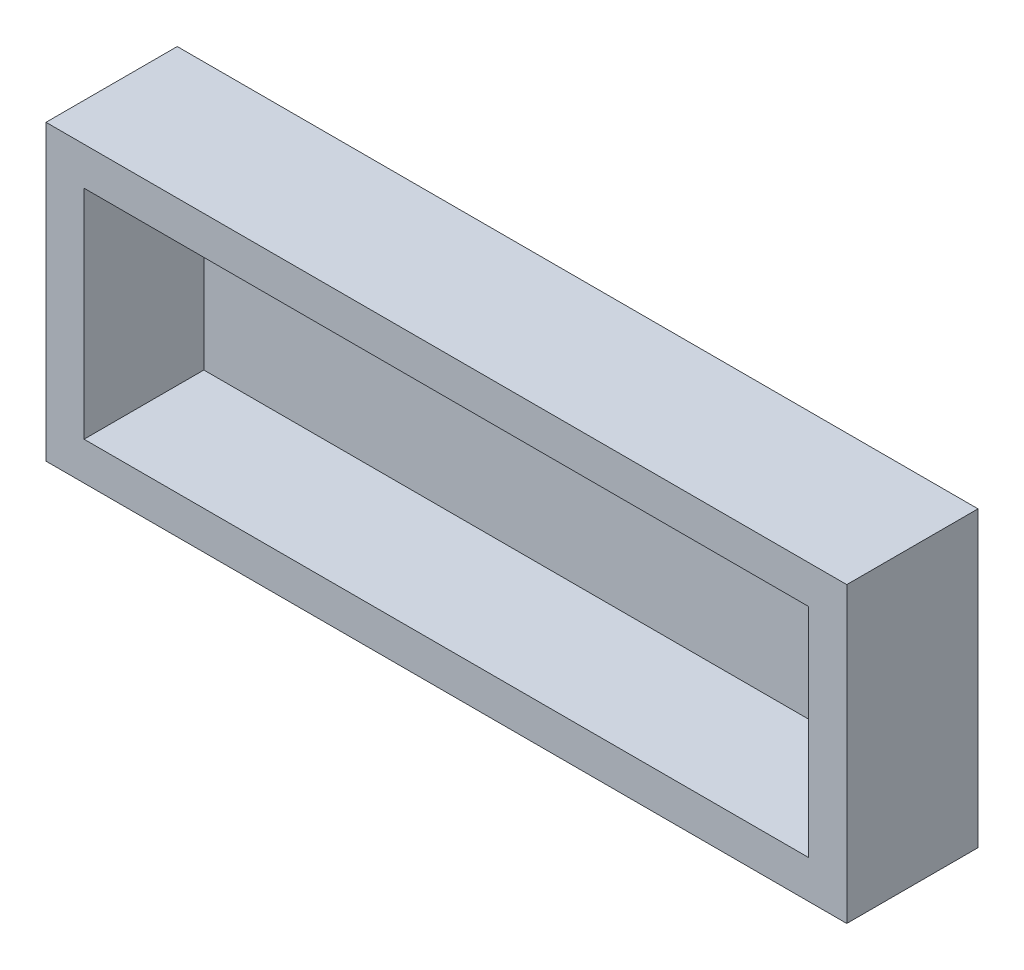
SolidWorks part; units mm, degrees
ref_plane "Front Plane" through (0, 0, 0) normal (0, 0, 1) x (1, 0, 0)
ref_plane "Top Plane" through (0, 0, 0) normal (0, 1, 0) x (1, 0, 0)
ref_plane "Right Plane" through (0, 0, 0) normal (1, 0, 0) x (0, 0, -1)
sketch "Model" plane through (0, 0, 0) normal (0, 0, 1) x (1, 0, 0)
  line L0 (188.597, 57.4075) -> (188.753, 57.4008)
  line L1 (188.753, 57.4008) -> (188.908, 57.3828)
  line L2 (188.908, 57.3828) -> (189.063, 57.3525)
  line L3 (189.063, 57.3525) -> (189.214, 57.3098)
  line L4 (189.214, 57.3098) -> (189.362, 57.2548)
  line L5 (189.362, 57.2548) -> (189.504, 57.1899)
  line L6 (189.504, 57.1899) -> (189.64, 57.113)
  line L7 (189.64, 57.113) -> (189.771, 57.0258)
  line L8 (189.771, 57.0258) -> (189.895, 56.9281)
  line L9 (189.895, 56.9281) -> (190.011, 56.8219)
  line L10 (190.011, 56.8219) -> (190.117, 56.7062)
  line L11 (190.117, 56.7062) -> (190.215, 56.5838)
  line L12 (190.215, 56.5838) -> (190.302, 56.4526)
  line L13 (190.302, 56.4526) -> (190.379, 56.315)
  line L14 (190.379, 56.315) -> (190.444, 56.1728)
  line L15 (190.444, 56.1728) -> (190.499, 56.0268)
  line L16 (190.499, 56.0268) -> (190.54, 55.874)
  line L17 (190.54, 55.874) -> (190.572, 55.7209)
  line L18 (190.572, 55.7209) -> (190.59, 55.5639)
  line L19 (190.59, 55.5639) -> (190.596, 55.4069)
  line L20 (190.596, 55.4069) -> (190.596, 2.2572)
  line L21 (190.596, 2.2572) -> (190.59, 2.1001)
  line L22 (190.59, 2.1001) -> (190.572, 1.9444)
  line L23 (190.572, 1.9444) -> (190.54, 1.7901)
  line L24 (190.54, 1.7901) -> (190.499, 1.6385)
  line L25 (190.499, 1.6385) -> (190.444, 1.491)
  line L26 (190.444, 1.491) -> (190.379, 1.3491)
  line L27 (190.379, 1.3491) -> (190.302, 1.2127)
  line L28 (190.302, 1.2127) -> (190.215, 1.0818)
  line L29 (190.215, 1.0818) -> (190.117, 0.9577)
  line L30 (190.117, 0.9577) -> (190.011, 0.842)
  line L31 (190.011, 0.842) -> (189.895, 0.7359)
  line L32 (189.895, 0.7359) -> (189.771, 0.638)
  line L33 (189.771, 0.638) -> (189.64, 0.5512)
  line L34 (189.64, 0.5512) -> (189.504, 0.474)
  line L35 (189.504, 0.474) -> (189.362, 0.4093)
  line L36 (189.362, 0.4093) -> (189.214, 0.3542)
  line L37 (189.214, 0.3542) -> (189.063, 0.3128)
  line L38 (189.063, 0.3128) -> (188.908, 0.2811)
  line L39 (188.908, 0.2811) -> (188.753, 0.2632)
  line L40 (188.753, 0.2632) -> (188.597, 0.2563)
  line L41 (188.597, 0.2563) -> (2.096, 0.2577)
  line L42 (2.096, 0.2577) -> (1.9389, 0.2632)
  line L43 (1.9389, 0.2632) -> (1.7818, 0.2811)
  line L44 (1.7818, 0.2811) -> (1.6288, 0.3128)
  line L45 (1.6288, 0.3128) -> (1.4759, 0.3542)
  line L46 (1.4759, 0.3542) -> (1.3298, 0.4093)
  line L47 (1.3298, 0.4093) -> (1.1879, 0.474)
  line L48 (1.1879, 0.474) -> (1.0501, 0.5512)
  line L49 (1.0501, 0.5512) -> (0.9192, 0.638)
  line L50 (0.9192, 0.638) -> (0.7965, 0.7359)
  line L51 (0.7965, 0.7359) -> (0.6808, 0.842)
  line L52 (0.6808, 0.842) -> (0.5746, 0.9577)
  line L53 (0.5746, 0.9577) -> (0.4768, 1.0818)
  line L54 (0.4768, 1.0818) -> (0.39, 1.2127)
  line L55 (0.39, 1.2127) -> (0.3128, 1.3491)
  line L56 (0.3128, 1.3491) -> (0.248, 1.491)
  line L57 (0.248, 1.491) -> (0.1929, 1.6385)
  line L58 (0.1929, 1.6385) -> (0.1502, 1.7901)
  line L59 (0.1502, 1.7901) -> (0.1199, 1.9444)
  line L60 (0.1199, 1.9444) -> (0.102, 2.1001)
  line L61 (0.102, 2.1001) -> (0.0951, 2.2572)
  line L62 (0.0951, 2.2572) -> (0.0951, 55.4069)
  line L63 (0.0951, 55.4069) -> (0.102, 55.5639)
  line L64 (0.102, 55.5639) -> (0.1199, 55.7209)
  line L65 (0.1199, 55.7209) -> (0.1502, 55.874)
  line L66 (0.1502, 55.874) -> (0.1929, 56.0268)
  line L67 (0.1929, 56.0268) -> (0.248, 56.1728)
  line L68 (0.248, 56.1728) -> (0.3128, 56.315)
  line L69 (0.3128, 56.315) -> (0.39, 56.4526)
  line L70 (0.39, 56.4526) -> (0.4768, 56.5838)
  line L71 (0.4768, 56.5838) -> (0.5746, 56.7062)
  line L72 (0.5746, 56.7062) -> (0.6808, 56.8219)
  line L73 (0.6808, 56.8219) -> (0.7965, 56.9281)
  line L74 (0.7965, 56.9281) -> (0.9192, 57.0258)
  line L75 (0.9192, 57.0258) -> (1.0501, 57.113)
  line L76 (1.0501, 57.113) -> (1.1879, 57.1899)
  line L77 (1.1879, 57.1899) -> (1.3298, 57.2548)
  line L78 (1.3298, 57.2548) -> (1.4759, 57.3098)
  line L79 (1.4759, 57.3098) -> (1.6288, 57.3525)
  line L80 (1.6288, 57.3525) -> (1.7818, 57.3828)
  line L81 (1.7818, 57.3828) -> (1.9389, 57.4008)
  line L82 (1.9389, 57.4008) -> (2.096, 57.4075)
  line L83 (2.096, 57.4075) -> (188.597, 57.4075)
  line L84 (174.071, 16.7817) -> (188.07, 16.7817)
  line L85 (188.07, 16.7817) -> (188.07, 2.7823)
  line L86 (188.07, 2.7823) -> (174.071, 2.7823)
  line L87 (174.071, 2.7823) -> (174.071, 16.7817)
  line L88 (155.021, 16.7817) -> (169.02, 16.7817)
  line L89 (169.02, 16.7817) -> (169.02, 2.7823)
  line L90 (169.02, 2.7823) -> (155.021, 2.7823)
  line L91 (155.021, 2.7823) -> (155.021, 16.7817)
  line L92 (135.971, 16.7817) -> (149.97, 16.7817)
  line L93 (149.97, 16.7817) -> (149.97, 2.7823)
  line L94 (149.97, 2.7823) -> (135.971, 2.7823)
  line L95 (135.971, 2.7823) -> (135.971, 16.7817)
  line L96 (116.92, 16.7817) -> (130.92, 16.7817)
  line L97 (130.92, 16.7817) -> (130.92, 2.7823)
  line L98 (130.92, 2.7823) -> (116.92, 2.7823)
  line L99 (116.92, 2.7823) -> (116.92, 16.7817)
  line L100 (97.8697, 16.7817) -> (111.869, 16.7817)
  line L101 (111.869, 16.7817) -> (111.869, 2.7823)
  line L102 (111.869, 2.7823) -> (97.8697, 2.7823)
  line L103 (97.8697, 2.7823) -> (97.8697, 16.7817)
  line L104 (78.8211, 16.7817) -> (92.8204, 16.7817)
  line L105 (92.8204, 16.7817) -> (92.8204, 2.7823)
  line L106 (92.8204, 2.7823) -> (78.8211, 2.7823)
  line L107 (78.8211, 2.7823) -> (78.8211, 16.7817)
  line L108 (59.7711, 16.7817) -> (73.7704, 16.7817)
  line L109 (73.7704, 16.7817) -> (73.7704, 2.7823)
  line L110 (73.7704, 2.7823) -> (59.7711, 2.7823)
  line L111 (59.7711, 2.7823) -> (59.7711, 16.7817)
  line L112 (40.7211, 16.7817) -> (54.7204, 16.7817)
  line L113 (54.7204, 16.7817) -> (54.7204, 2.7823)
  line L114 (54.7204, 2.7823) -> (40.7211, 2.7823)
  line L115 (40.7211, 2.7823) -> (40.7211, 16.7817)
  line L116 (21.671, 16.7817) -> (35.6704, 16.7817)
  line L117 (35.6704, 16.7817) -> (35.6704, 2.7823)
  line L118 (35.6704, 2.7823) -> (21.671, 2.7823)
  line L119 (21.671, 2.7823) -> (21.671, 16.7817)
  line L120 (2.621, 16.7817) -> (16.6205, 16.7817)
  line L121 (16.6205, 16.7817) -> (16.6205, 2.7823)
  line L122 (16.6205, 2.7823) -> (2.621, 2.7823)
  line L123 (2.621, 2.7823) -> (2.621, 16.7817)
  line L124 (174.071, 35.8316) -> (188.07, 35.8316)
  line L125 (188.07, 35.8316) -> (188.07, 21.8323)
  line L126 (188.07, 21.8323) -> (174.071, 21.8323)
  line L127 (174.071, 21.8323) -> (174.071, 35.8316)
  line L128 (155.021, 35.8316) -> (169.02, 35.8316)
  line L129 (169.02, 35.8316) -> (169.02, 21.8323)
  line L130 (169.02, 21.8323) -> (155.021, 21.8323)
  line L131 (155.021, 21.8323) -> (155.021, 35.8316)
  line L132 (135.971, 35.8316) -> (149.97, 35.8316)
  line L133 (149.97, 35.8316) -> (149.97, 21.8323)
  line L134 (149.97, 21.8323) -> (135.971, 21.8323)
  line L135 (135.971, 21.8323) -> (135.971, 35.8316)
  line L136 (116.92, 35.8316) -> (130.92, 35.8316)
  line L137 (130.92, 35.8316) -> (130.92, 21.8323)
  line L138 (130.92, 21.8323) -> (116.92, 21.8323)
  line L139 (116.92, 21.8323) -> (116.92, 35.8316)
  line L140 (97.8697, 35.8316) -> (111.869, 35.8316)
  line L141 (111.869, 35.8316) -> (111.869, 21.8323)
  line L142 (111.869, 21.8323) -> (97.8697, 21.8323)
  line L143 (97.8697, 21.8323) -> (97.8697, 35.8316)
  line L144 (78.8211, 35.8316) -> (92.8204, 35.8316)
  line L145 (92.8204, 35.8316) -> (92.8204, 21.8323)
  line L146 (92.8204, 21.8323) -> (78.8211, 21.8323)
  line L147 (78.8211, 21.8323) -> (78.8211, 35.8316)
  line L148 (59.7711, 35.8316) -> (73.7704, 35.8316)
  line L149 (73.7704, 35.8316) -> (73.7704, 21.8323)
  line L150 (73.7704, 21.8323) -> (59.7711, 21.8323)
  line L151 (59.7711, 21.8323) -> (59.7711, 35.8316)
  line L152 (40.7211, 35.8316) -> (54.7204, 35.8316)
  line L153 (54.7204, 35.8316) -> (54.7204, 21.8323)
  line L154 (54.7204, 21.8323) -> (40.7211, 21.8323)
  line L155 (40.7211, 21.8323) -> (40.7211, 35.8316)
  line L156 (21.671, 35.8316) -> (35.6704, 35.8316)
  line L157 (35.6704, 35.8316) -> (35.6704, 21.8323)
  line L158 (35.6704, 21.8323) -> (21.671, 21.8323)
  line L159 (21.671, 21.8323) -> (21.671, 35.8316)
  line L160 (2.621, 35.8316) -> (16.6205, 35.8316)
  line L161 (16.6205, 35.8316) -> (16.6205, 21.8323)
  line L162 (16.6205, 21.8323) -> (2.621, 21.8323)
  line L163 (2.621, 21.8323) -> (2.621, 35.8316)
  line L164 (174.071, 54.8816) -> (188.07, 54.8816)
  line L165 (188.07, 54.8816) -> (188.07, 40.8824)
  line L166 (188.07, 40.8824) -> (174.071, 40.8824)
  line L167 (174.071, 40.8824) -> (174.071, 54.8816)
  line L168 (155.021, 54.8816) -> (169.02, 54.8816)
  line L169 (169.02, 54.8816) -> (169.02, 40.8824)
  line L170 (169.02, 40.8824) -> (155.021, 40.8824)
  line L171 (155.021, 40.8824) -> (155.021, 54.8816)
  line L172 (135.971, 54.8816) -> (149.97, 54.8816)
  line L173 (149.97, 54.8816) -> (149.97, 40.8824)
  line L174 (149.97, 40.8824) -> (135.971, 40.8824)
  line L175 (135.971, 40.8824) -> (135.971, 54.8816)
  line L176 (116.92, 54.8816) -> (130.92, 54.8816)
  line L177 (130.92, 54.8816) -> (130.92, 40.8824)
  line L178 (130.92, 40.8824) -> (116.92, 40.8824)
  line L179 (116.92, 40.8824) -> (116.92, 54.8816)
  line L180 (97.8697, 54.8816) -> (111.869, 54.8816)
  line L181 (111.869, 54.8816) -> (111.869, 40.8824)
  line L182 (111.869, 40.8824) -> (97.8697, 40.8824)
  line L183 (97.8697, 40.8824) -> (97.8697, 54.8816)
  line L184 (78.8211, 54.8816) -> (92.8204, 54.8816)
  line L185 (92.8204, 54.8816) -> (92.8204, 40.8824)
  line L186 (92.8204, 40.8824) -> (78.8211, 40.8824)
  line L187 (78.8211, 40.8824) -> (78.8211, 54.8816)
  line L188 (59.7711, 54.8816) -> (73.7704, 54.8816)
  line L189 (73.7704, 54.8816) -> (73.7704, 40.8824)
  line L190 (73.7704, 40.8824) -> (59.7711, 40.8824)
  line L191 (59.7711, 40.8824) -> (59.7711, 54.8816)
  line L192 (40.7211, 54.8816) -> (54.7204, 54.8816)
  line L193 (54.7204, 54.8816) -> (54.7204, 40.8824)
  line L194 (54.7204, 40.8824) -> (40.7211, 40.8824)
  line L195 (40.7211, 40.8824) -> (40.7211, 54.8816)
  line L196 (21.671, 54.8816) -> (35.6704, 54.8816)
  line L197 (35.6704, 54.8816) -> (35.6704, 40.8824)
  line L198 (35.6704, 40.8824) -> (21.671, 40.8824)
  line L199 (21.671, 40.8824) -> (21.671, 54.8816)
  line L200 (2.621, 54.8816) -> (16.6205, 54.8816)
  line L201 (16.6205, 54.8816) -> (16.6205, 40.8824)
  line L202 (16.6205, 40.8824) -> (2.621, 40.8824)
  line L203 (2.621, 40.8824) -> (2.621, 54.8816)
sketch "草图2" plane through (0, 0, 0) normal (0, 0, 1) x (1, 0, 0)
  line L0 (0.0951, 28.8321) -> (190.596, 28.8321) construction
  line L1 (0.0951, 2.2572) -> (0.0951, 55.4069) construction
  line L2 (190.596, 55.4069) -> (190.596, 2.2572) construction
  line L3 (95.3465, 57.4075) -> (95.3465, 0.257) construction
  line L4 (2.096, 57.4075) -> (188.597, 57.4075) construction
  line L5 (188.597, 0.2563) -> (2.096, 0.2577) construction
  line L7 (200.596, -9.7432) -> (-9.9049, -9.7432)
  line L8 (200.596, -9.7432) -> (200.596, 67.4073)
  line L9 (200.596, 67.4073) -> (-9.9049, 67.4073)
  line L10 (-9.9049, -9.7432) -> (-9.9049, 67.4073)
  line L11 (200.596, -9.7432) -> (-9.9049, 67.4073) construction
  line L12 (200.596, 67.4073) -> (-9.9049, -9.7432) construction
  point P12 (95.3455, 28.8321)
  dimension "D1" = 190.5009
  dimension "D2" = 57.1505
  dimension "D3" = 77.1505
  dimension "D4" = 210.5009
extrude "凸台-拉伸1" add sketch "草图2" along normal blind 34.5
shell "抽壳1" thickness 10
sketch "草图3" plane through (0, 0, 0) normal (0, 0, 1) x (1, 0, 0)
  line L3 (35.6704, 21.8323) -> (40.7211, 16.7817) construction
  line L4 (40.7211, 16.7817) -> (40.7211, 21.8323) construction
  line L5 (40.7211, 21.8323) -> (35.6704, 16.7817) construction
  line L6 (149.97, 35.8316) -> (155.021, 40.8824) construction
  line L8 (149.97, 16.7817) -> (155.021, 21.8323) construction
  circle A0 centre (152.4955, 38.357) radius 2.7421
  circle A1 centre (152.4955, 19.1108) radius 3.3242
  circle A2 centre (38.1958, 38.357) radius 2
  circle A3 centre (38.1958, 19.307) radius 2.8734
  dimension "D1" = 4
extrude "切除-拉伸8" cut sketch "草图3" along normal blind 3 contours A2
